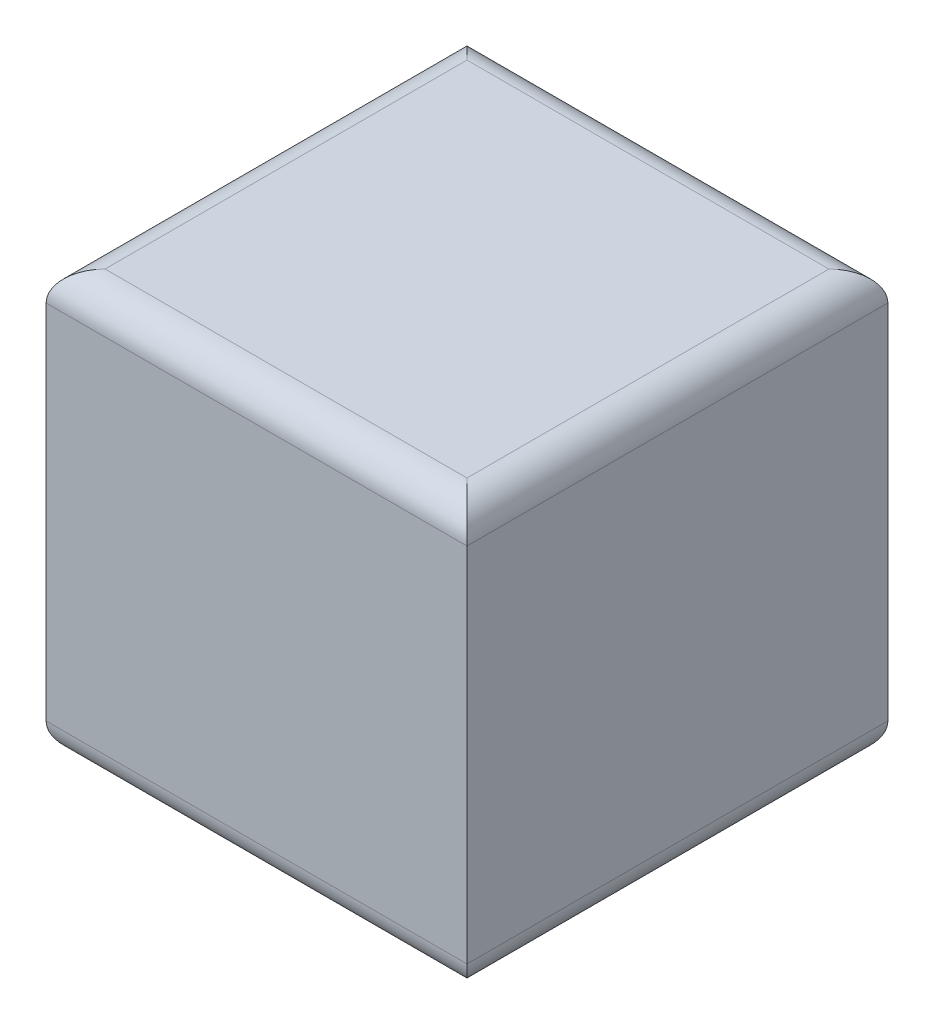
SolidWorks part; units mm, degrees
ref_plane "Front Plane" through (0, 0, 0) normal (0, 0, 1) x (1, 0, 0)
ref_plane "Top Plane" through (0, 0, 0) normal (0, 1, 0) x (1, 0, 0)
ref_plane "Right Plane" through (0, 0, 0) normal (1, 0, 0) x (0, 0, -1)
sketch "Sketch1" plane through (0, 0, 0) normal (0, 1, 0) x (1, 0, 0)
  line L1 (0, 0) -> (1000, 0)
  line L2 (0, 0) -> (0, 1000)
  line L3 (0, 1000) -> (1000, 1000)
  line L4 (1000, 0) -> (1000, 1000)
  dimension "D1" = 1000
  dimension "D2" = 1000
extrude "Boss-Extrude2" add sketch "Sketch1" along normal blind 1000
fillet "Fillet2" radius 70 8 edges at (500, 1000, -1000) (1000, 1000, -500) (500, 1000, 0) (0, 1000, -500) (500, 0, 0) (1000, 0, -500) (500, 0, -1000) (0, 0, -500)
